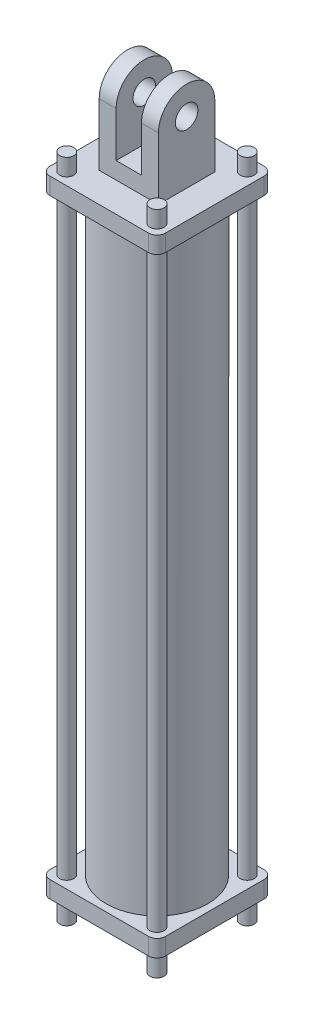
SolidWorks part; units mm, degrees
ref_plane "Front Plane" through (0, 0, 0) normal (0, 0, 1) x (1, 0, 0)
ref_plane "Top Plane" through (0, 0, 0) normal (0, 1, 0) x (1, 0, 0)
ref_plane "Right Plane" through (0, 0, 0) normal (1, 0, 0) x (0, 0, -1)
sketch "Sketch1" plane through (0, 0, 0) normal (0, 1, 0) x (1, 0, 0)
  line L1 (-65.0875, 65.0875) -> (65.0875, 65.0875)
  line L2 (-65.0875, 65.0875) -> (-65.0875, -65.0875)
  line L3 (-65.0875, -65.0875) -> (65.0875, -65.0875)
  line L4 (65.0875, 65.0875) -> (65.0875, -65.0875)
  line L5 (-65.0875, 65.0875) -> (65.0875, -65.0875) construction
  line L6 (-65.0875, -65.0875) -> (65.0875, 65.0875) construction
  point P0 (0, 0)
  dimension "D1" = 130.175
  dimension "D2" = 130.175
extrude "Boss-Extrude1" add sketch "Sketch1" along normal blind 19.05
sketch "Sketch2" plane through (0, 19.05, 0) normal (0, 1, 0) x (1, 0, 0)
  line L0 (-50.8, -50.8) -> (-50.8, 50.8) construction
  line L1 (-50.8, 50.8) -> (50.8, 50.8) construction
  line L2 (50.8, 50.8) -> (50.8, -50.8) construction
  line L3 (50.8, -50.8) -> (-50.8, -50.8) construction
  line L4 (-50.8, 0) -> (0, 0) construction
  line L5 (0, 0) -> (0, 50.8) construction
  circle A0 centre (-50.8, 50.8) radius 7.9375
  circle A1 centre (50.8, 50.8) radius 7.9375
  circle A2 centre (50.8, -50.8) radius 7.9375
  circle A3 centre (-50.8, -50.8) radius 7.9375
  dimension "D1" = 15.875
  dimension "D2" = 101.6
  dimension "D3" = 101.6
extrude "Cut-Extrude1" cut sketch "Sketch2" against normal up to next
sketch "Sketch3" plane through (0, 0, 0) normal (1, 0, 0) x (0, 0, -1)
  line L0 (-31.75, 19.05) -> (-31.75, 88.9)
  line L2 (-65.0875, 19.05) -> (65.0875, 19.05) construction
  line L3 (31.75, 19.05) -> (31.75, 88.9)
  line L4 (-31.75, 19.05) -> (31.75, 19.05)
  line L5 (0, 88.9) -> (0, 0) construction
  line L6 (-31.75, 88.9) -> (31.75, 88.9) construction
  arc A0 (-31.75, 88.9) -> (31.75, 88.9) centre (0, 88.9) cw
  circle A1 centre (0, 88.9) radius 12.7
  dimension "D2" = 25.4
  dimension "D3" = 31.75
  dimension "D1" = 69.85
extrude "Boss-Extrude2" add sketch "Sketch3" along normal mid plane 66.675
sketch "Sketch4" plane through (0, 0, 31.75) normal (0, 0, 1) x (1, 0, 0)
  line L0 (33.3375, 120.65) -> (-33.3375, 120.65) construction
  line L1 (-14.2875, 120.65) -> (14.2875, 120.65)
  line L2 (-14.2875, 120.65) -> (-14.2875, 38.1)
  line L3 (-14.2875, 38.1) -> (14.2875, 38.1)
  line L4 (14.2875, 120.65) -> (14.2875, 38.1)
  line L6 (0, 38.1) -> (0, 0) construction
  dimension "D1" = 28.575
  dimension "D2" = 38.1
extrude "Cut-Extrude2" cut sketch "Sketch4" against normal up to next
sketch "Sketch5" plane through (0, 0, 0) normal (0, -1, 0) x (1, 0, 0)
  circle A0 centre (0, 0) radius 57.15
  circle A1 centre (0, 0) radius 50.8
  dimension "D1" = 101.6
  dimension "D2" = 114.3
extrude "Boss-Extrude3" add sketch "Sketch5" along normal blind 666.75
fillet "Fillet1" radius 9.525 4 edges at (-65.0875, 9.525, -65.0875) (65.0875, 9.525, -65.0875) (-65.0875, 9.525, 65.0875) (65.0875, 9.525, 65.0875)
sketch "Sketch6" plane through (0, -666.75, 0) normal (0, -1, 0) x (1, 0, 0)
  line L4 (-65.0875, 55.5625) -> (-65.0875, -55.5625)
  line L5 (-55.5625, -65.0875) -> (55.5625, -65.0875)
  line L6 (65.0875, -55.5625) -> (65.0875, 55.5625)
  line L7 (55.5625, 65.0875) -> (-55.5625, 65.0875)
  line L8 (-65.0875, 55.5625) -> (-65.0875, -55.5625)
  line L9 (-55.5625, -65.0875) -> (55.5625, -65.0875)
  line L10 (65.0875, -55.5625) -> (65.0875, 55.5625)
  line L11 (55.5625, 65.0875) -> (-55.5625, 65.0875)
  circle A0 centre (-50.8, 50.8) radius 7.9375 construction
  circle A1 centre (50.8, 50.8) radius 7.9375 construction
  circle A2 centre (50.8, -50.8) radius 7.9375 construction
  circle A3 centre (-50.8, -50.8) radius 7.9375 construction
  arc A4 (-65.0875, -55.5625) -> (-55.5625, -65.0875) centre (-55.5625, -55.5625) ccw
  arc A5 (55.5625, -65.0875) -> (65.0875, -55.5625) centre (55.5625, -55.5625) ccw
  arc A6 (65.0875, 55.5625) -> (55.5625, 65.0875) centre (55.5625, 55.5625) ccw
  arc A7 (-55.5625, 65.0875) -> (-65.0875, 55.5625) centre (-55.5625, 55.5625) ccw
  arc A8 (-65.0875, -55.5625) -> (-55.5625, -65.0875) centre (-55.5625, -55.5625) ccw
  arc A9 (55.5625, -65.0875) -> (65.0875, -55.5625) centre (55.5625, -55.5625) ccw
  arc A10 (65.0875, 55.5625) -> (55.5625, 65.0875) centre (55.5625, 55.5625) ccw
  arc A11 (-55.5625, 65.0875) -> (-65.0875, 55.5625) centre (-55.5625, 55.5625) ccw
  circle A12 centre (-50.8, 50.8) radius 7.9375
  circle A13 centre (50.8, 50.8) radius 7.9375
  circle A14 centre (50.8, -50.8) radius 7.9375
  circle A15 centre (-50.8, -50.8) radius 7.9375
  dimension "D1" = 0
extrude "Boss-Extrude4" add sketch "Sketch6" along normal blind 19.05
sketch "Sketch7" plane through (0, -685.8, 0) normal (0, -1, 0) x (1, 0, 0)
  circle A0 centre (0, 0) radius 25.4
  dimension "D1" = 50.8
extrude "Cut-Extrude3" cut sketch "Sketch7" against normal up to next
sketch "Sketch8" plane through (0, 19.05, 0) normal (0, 1, 0) x (1, 0, 0)
  circle A0 centre (-50.8, 50.8) radius 7.9375 construction
  circle A1 centre (50.8, 50.8) radius 7.9375 construction
  circle A2 centre (50.8, -50.8) radius 7.9375 construction
  circle A3 centre (-50.8, -50.8) radius 7.9375 construction
  circle A4 centre (-50.8, 50.8) radius 7.9375
  circle A5 centre (50.8, 50.8) radius 7.9375
  circle A6 centre (50.8, -50.8) radius 7.9375
  circle A7 centre (-50.8, -50.8) radius 7.9375
extrude "Boss-Extrude5" add sketch "Sketch8" along normal blind 19.05 and the other way blind 730.25
sketch "Sketch9" plane through (0, 0, 0) normal (1, 0, 0) x (0, 0, -1)
  point P0 (0, 88.9)
sketch "Sketch10" plane through (0, 0, 0) normal (1, 0, 0) x (0, 0, -1)
  point P0 (0, 88.9)
